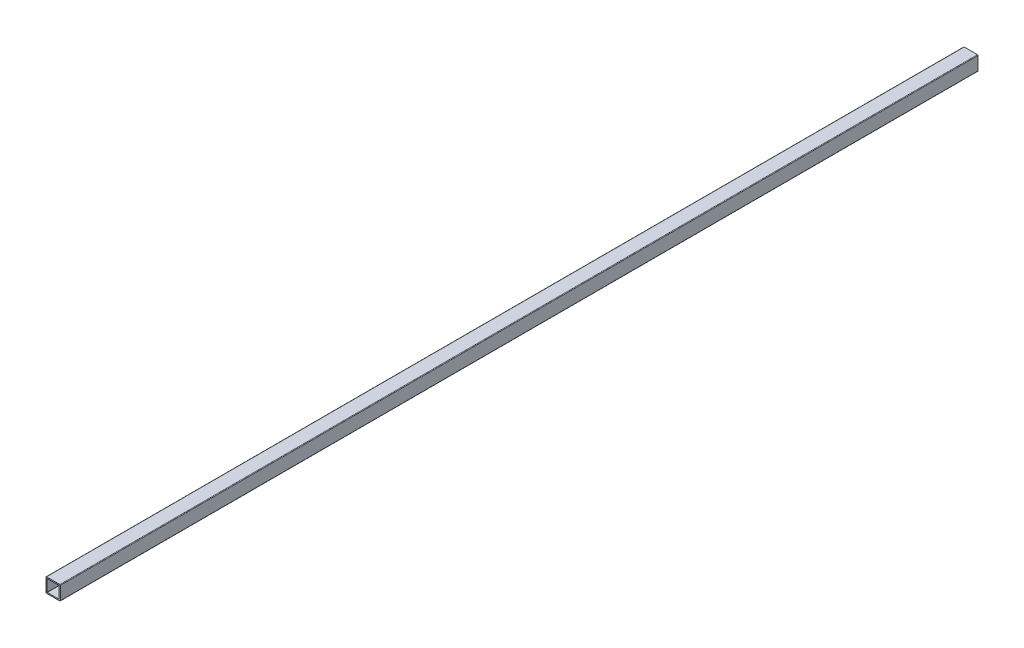
SolidWorks part; units mm, degrees
ref_plane "Front Plane" through (0, 0, 0) normal (0, 0, 1) x (1, 0, 0)
ref_plane "Top Plane" through (0, 0, 0) normal (0, 1, 0) x (1, 0, 0)
ref_plane "Right Plane" through (0, 0, 0) normal (1, 0, 0) x (0, 0, -1)
sketch "Sketch1" plane through (0, 0, 0) normal (0, 0, 1) x (1, 0, 0)
  line L1 (-19.05, -19.05) -> (19.05, -19.05)
  line L2 (-19.05, -19.05) -> (-19.05, 19.05)
  line L3 (-19.05, 19.05) -> (19.05, 19.05)
  line L4 (19.05, -19.05) -> (19.05, 19.05)
  line L5 (0, 19.05) -> (0, -19.05) construction
  line L6 (-19.05, 0) -> (19.05, 0) construction
  line L7 (-16.002, -16.002) -> (16.002, -16.002)
  line L8 (-16.002, -16.002) -> (-16.002, 16.002)
  line L9 (-16.002, 16.002) -> (16.002, 16.002)
  line L10 (16.002, -16.002) -> (16.002, 16.002)
  line L11 (0, 16.002) -> (0, -16.002) construction
  line L12 (-16.002, 0) -> (16.002, 0) construction
  point P0 (0, 0)
  point P4 (0, 0)
  dimension "Outside Height" = 38.1
  dimension "Wall Thickness" = 3.048
  dimension "Outside Width" = 38.1
  dimension "Inside Height" = 32.004
  dimension "Inside Width" = 32.004
sketch "Sketch2" plane through (0, 0, 0) normal (1, 0, 0) x (0, 0, -1)
  line L0 (-1219.2, 0) -> (1219.2, 0) construction
  line L2 (-1219.2, 19.05) -> (1219.2, 19.05)
  line L3 (-1219.2, 19.05) -> (-1219.2, -19.05)
  line L4 (-1219.2, -19.05) -> (1219.2, -19.05)
  line L5 (1219.2, 19.05) -> (1219.2, -19.05)
  point P7 (1143, 0)
  point P10 (-1143, 0)
  dimension "Length" = 2438.4
  dimension "Breakline" = 76.2
  dimension "D2" = 76.2
sketch "Sketch3" plane through (0, 0, 0) normal (0, 0, 1) x (1, 0, 0)
  line L0 (-16.002, -16.002) -> (-16.002, 16.002) construction
  line L1 (-16.002, -16.002) -> (16.002, -16.002) construction
  line L2 (16.002, -16.002) -> (16.002, 16.002) construction
  line L3 (-16.002, 16.002) -> (16.002, 16.002) construction
  line L4 (-19.05, -19.05) -> (-19.05, 19.05) construction
  line L5 (-19.05, -19.05) -> (19.05, -19.05) construction
  line L6 (19.05, -19.05) -> (19.05, 19.05) construction
  line L7 (-19.05, 19.05) -> (19.05, 19.05) construction
  line L8 (-16.002, -16.002) -> (-16.002, 16.002)
  line L9 (-16.002, -16.002) -> (16.002, -16.002)
  line L10 (16.002, -16.002) -> (16.002, 16.002)
  line L11 (-16.002, 16.002) -> (16.002, 16.002)
  line L12 (-19.05, -19.05) -> (-19.05, 19.05)
  line L13 (-19.05, -19.05) -> (19.05, -19.05)
  line L14 (19.05, -19.05) -> (19.05, 19.05)
  line L15 (-19.05, 19.05) -> (19.05, 19.05)
extrude "Boss-Extrude1" add sketch "Sketch3" along normal up to vertex (1219.2 mm away) and the other way up to vertex (1219.2 mm away) up to point (0, 19.05, 1219.2) other way up to point (0, 19.05, -1219.2)
fillet "Fillet1" radius 1.524 4 edges at (-19.05, -19.05, 0) (19.05, -19.05, 0) (-19.05, 19.05, 0) (19.05, 19.05, 0)
fillet "Fillet2" radius 0.3048 4 edges at (16.002, 16.002, 0) (-16.002, 16.002, 0) (16.002, -16.002, 0) (-16.002, -16.002, 0)
equation "\"D2@Sketch2\" = \"Breakline@Sketch2\""
equation "\"D1@Fillet1\"=\"Wall Thickness@Sketch1\"/2"
equation "\"D1@Fillet2\"=\"Wall Thickness@Sketch1\"*.1"
